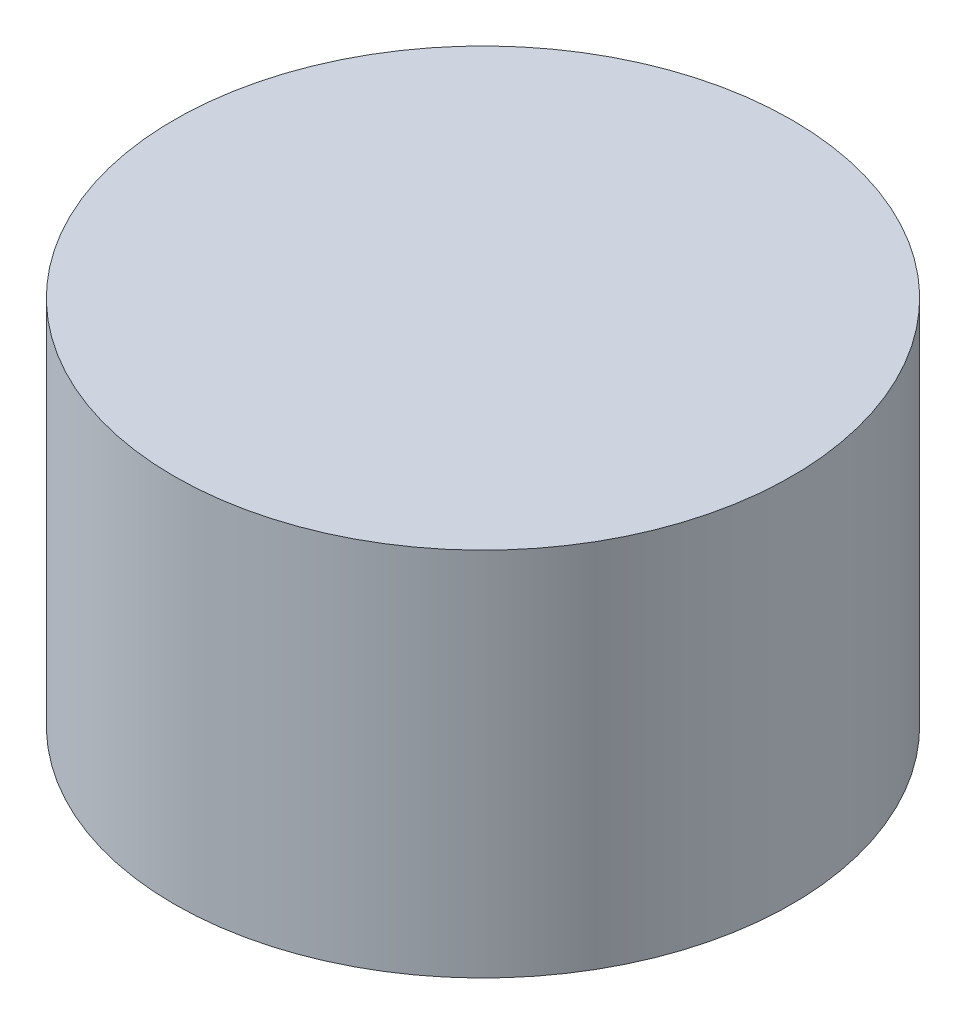
SolidWorks part; units mm, degrees
ref_plane "Front Plane" through (0, 0, 0) normal (0, 0, 1) x (1, 0, 0)
ref_plane "Top Plane" through (0, 0, 0) normal (0, 1, 0) x (1, 0, 0)
ref_plane "Right Plane" through (0, 0, 0) normal (1, 0, 0) x (0, 0, -1)
sketch "Sketch1" plane through (0, 0, 0) normal (0, 1, 0) x (1, 0, 0)
  circle A0 centre (0, 0) radius 5
  dimension "D1" = 10
extrude "Boss-Extrude1" add sketch "Sketch1" along normal blind 6
